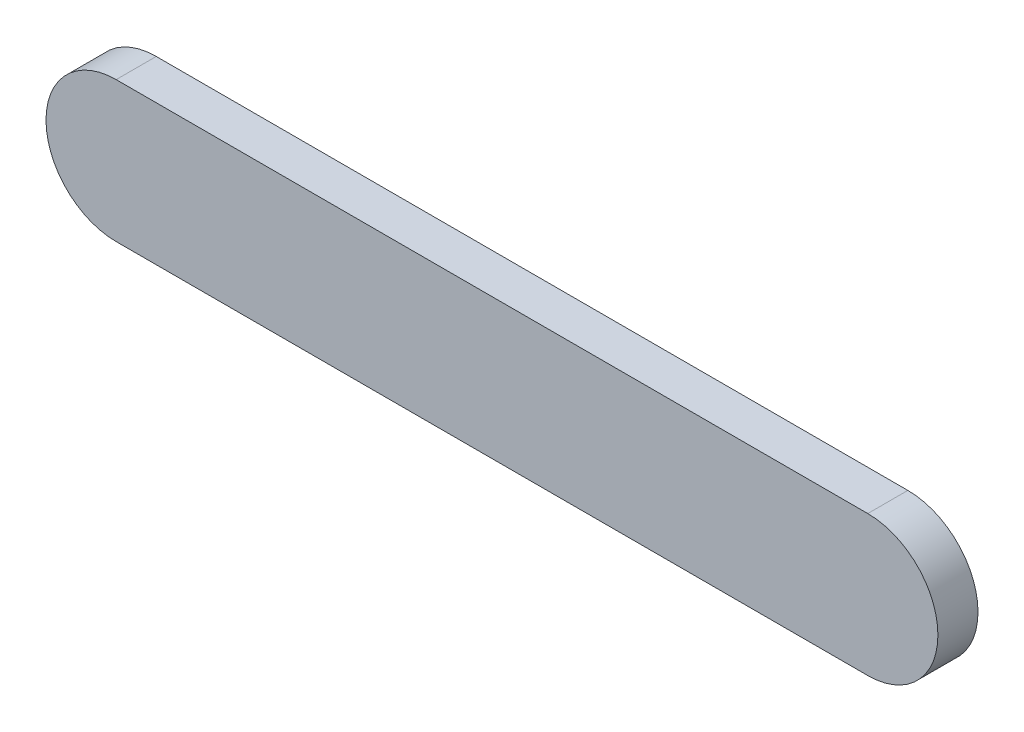
SolidWorks part; units mm, degrees
ref_plane "前视基准面" through (0, 0, 0) normal (0, 0, 1) x (1, 0, 0)
ref_plane "上视基准面" through (0, 0, 0) normal (0, 1, 0) x (1, 0, 0)
ref_plane "右视基准面" through (0, 0, 0) normal (1, 0, 0) x (0, 0, -1)
sketch "草图1" plane through (0, 0, 0) normal (0, 0, 1) x (1, 0, 0)
  line L1 (-112.5, 21) -> (112.5, 21)
  line L2 (-112.5, -21) -> (112.5, -21)
  arc A0 (-112.5, 21) -> (-112.5, -21) centre (-112.5, 0) ccw
  arc A1 (112.5, -21) -> (112.5, 21) centre (112.5, 0) ccw
  point P4 (0, 0)
  dimension "D2" = 42
  dimension "D1" = 225
extrude "凸台-拉伸1" add sketch "草图1" along normal blind 12
sketch "草图2" plane through (0, 0, 0) normal (0, 0, -1) x (-1, 0, 0)
  circle A0 centre (-112.5, 0) radius 21 construction
